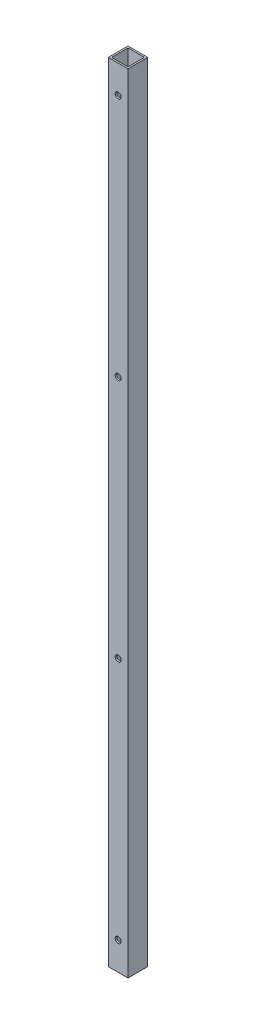
SolidWorks part; units mm, degrees
material "1060 Alloy"
ref_plane "Front Plane" through (0, 0, 0) normal (0, 0, 1) x (1, 0, 0)
ref_plane "Top Plane" through (0, 0, 0) normal (0, 1, 0) x (1, 0, 0)
ref_plane "Right Plane" through (0, 0, 0) normal (1, 0, 0) x (0, 0, -1)
sketch "Sketch1" plane through (0, 0, 0) normal (0, 1, 0) x (1, 0, 0)
  line L1 (-9.5, 9.5) -> (9.5, 9.5)
  line L2 (-9.5, 9.5) -> (-9.5, -9.5)
  line L3 (-9.5, -9.5) -> (9.5, -9.5)
  line L4 (9.5, 9.5) -> (9.5, -9.5)
  line L5 (-9.5, 9.5) -> (9.5, -9.5) construction
  line L6 (-9.5, -9.5) -> (9.5, 9.5) construction
  line L7 (-7.9375, 7.9375) -> (7.9375, 7.9375)
  line L8 (-7.9375, 7.9375) -> (-7.9375, -7.9375)
  line L9 (-7.9375, -7.9375) -> (7.9375, -7.9375)
  line L10 (7.9375, 7.9375) -> (7.9375, -7.9375)
  line L11 (-7.9375, 7.9375) -> (7.9375, -7.9375) construction
  line L12 (-7.9375, -7.9375) -> (7.9375, 7.9375) construction
  point P0 (0, 0)
  point P5 (0, 0)
  dimension "D1" = 19
  dimension "D2" = 19
  dimension "D3" = 15.875
  dimension "D4" = 15.875
extrude "Tube" add sketch "Sketch1" along normal blind 758.9266
sketch "Sketch2" plane through (0, 0, 9.5) normal (0, 0, 1) x (1, 0, 0)
  line L0 (0, 758.9266) -> (0, 777.9766) construction
  line L1 (0, 777.9766) -> (0, 781.05) construction
  line L6 (0, 731.925) -> (0, 758.9266) construction
  line L7 (-9.5, 758.9266) -> (9.5, 758.9266) construction
  circle A2 centre (0, 731.925) radius 2.8956
  dimension "D1" = 5.7912
  dimension "D2" = 19.05
  dimension "D3" = 3.0734
  dimension "D4" = 49.125
extrude "Side Wall Holes" cut sketch "Sketch2" against normal through all
pattern_linear "LPattern1" count 4 spacing 234.9745 along (0, -1, 0) of "Side Wall Holes"
sketch "Sketch3" plane through (-9.5, 0, 0) normal (-1, 0, 0) x (0, 0, 1)
  line L0 (-9.5, 758.9266) -> (9.5, 758.9266) construction
  line L1 (-123.9293, 379.4633) -> (189.6619, 379.4633) construction
  line L2 (-9.5, 0) -> (9.5, 0) construction
  circle A0 centre (0, 674.37) radius 4.7625
  circle A1 centre (0, 84.5566) radius 4.7625
  point P4 (0, 758.9266)
  dimension "D1" = 9.525
  dimension "D2" = 84.5566
extrude "Cut-Extrude1" cut sketch "Sketch3" against normal up to next and the other way through all
equation "\"Height\"= 32in"
equation "\"Width\"= 23in"
equation "\"Depth\"= 20in"
equation "\"Plexi\"= .121in"
equation "\"Cutwidth\"= .016in"
equation "\"Earsize\"= 1in + \"Cutwidth\" /2"
equation "\"Slotsize\" = 1in - \"CutWidth\" / 2"
equation "\"InnerWidth\" = \"Width\" - 2* \"Plexi\""
equation "\"InnerHeight\" = \"Height\" -2 * \"Plexi\""
equation "\"RearHoleSpacing\" = (\"Width\" - 2*\"RearHolesBorder\") / (\"RearNumHoles\"-1)"
equation "\"RivetDia\" = .228in"
equation "\"SlotDepth\" = \"Plexi\" + 0.75in + .005in"
equation "\"SideSlotWidth\"   = \"Plexi\"+.005in"
equation "\"D1@Sketch2\"=\"RivetDia\""
equation "\"D2@Sketch2\"=\"CornerCube\""
equation "\"SidePanelVertSpacing\" = (\"Height\"-2*(1.75-\"Plexi\")) / 5"
equation "\"MagnetThickness\"= 0.125in"
equation "\"MagnetDiameter\"= 12mm"
equation "\"DoorPlexi\" = \"Plexi\""
equation "\"Boxsize\" = .75in"
equation "\"Boxinner\" = .625in"
equation "\"CornerCube\" = 0.75in"
equation "\"FingerLength\" = 1.125in"
equation "\"InnerDepth\" = \"Depth\" - 2*\"Plexi\""
equation "\"RearNumHoles\" = 4"
equation "\"RearHolesBorder\" = 2.25"
equation "\"RearBarLength\" = (\"InnerWidth\"-2*\"CornerCube\")"
equation "\"RearTopNumHoles\" = 4"
equation "\"RearTopHolesBorder\" = 3.1"
equation "\"RearTopHolesSpacing\" = (\"Width\" - 2*\"RearTopHolesBorder\") / (\"RearTopNumHoles\"-1)"
equation "\"SideTopNumHoles\" = 4"
equation "\"SideTopHoleOffset\"=\"CornerCube\"+\"FingerLength\"+\"Plexi\"+.5"
equation "\"SideTopHoleSpacing\" = (\"TopBarDepth\"-2*\"SideTopHoleOffset\") / (\"SideTopNumHoles\"-1)"
equation "\"SideHorizNumHoles\" = 4"
equation "\"SideHorizHoleBorder\" = 1.50"
equation "\"SideHorizHoleSpacing\" = (\"TopBarDepth\"-2*\"SideHorizHoleBorder\") / (\"SideHorizNumHoles\"-1)"
equation "\"SideVertNumHoles\" = 4"
equation "\"SideVertHolesBorder\" = \"CornerCube\"+\"FingerLength\"+1.50"
equation "\"SideVertHoleSpacing\" = (\"SideVertBarLength\" - 2*(\"SideVertHolesBorder\"-\"Plexi\"-\"CornerCube\")) / (\"SideVertNumHoles\"-1)"
equation "\"BottomPanelSideHoleSpacing\" = (\"InnerDepth\"-2*(1.75-\"Plexi\")) / 4"
equation "\"FrontDoorGap\" = .1in"
equation "\"TopDepth\" = \"Depth\"-\"DoorPlexi\"-\"FrontDoorGap\""
equation "\"TopBarDepth\" = \"Depth\"-\"DoorPlexi\"-\"Plexi\"-2*\"MagnetThickness\"-2*\"CornerCube\""
equation "\"D3@Sketch2\"=\"Plexi\""
equation "\"D4@Sketch2\"=\"SideVertHolesBorder\""
equation "\"D3@LPattern1\"=\"SideVertHoleSpacing\""
equation "\"D1@LPattern1\"=\"SideVertNumHoles\""
equation "\"BasePlateThickness\" = 0.5in"
equation "\"SideVertBarLength\"=\"Height\"-\"BasePlateThickness\"-2*\"CornerCube\"-\"Plexi\""
equation "\"RearSideVertNumHoles\" = 4"
equation "\"RearSideVertHolesBorder\" = 2.4"
equation "\"RearSideVertHoleSpacing\" = (\"SideVertBarLength\" - 2*(\"RearSideVertHolesBorder\"-\"Plexi\"-\"CornerCube\")) / (\"RearSideVertNumHoles\"-1)"
equation "\"D1@Tube\"=\"SideVertBarLength\""
equation "\"D3@Sketch1\"=\"Boxinner\""
equation "\"D4@Sketch1\"=\"Boxinner\""
equation "\"EBWidth\" = 9in"
equation "\"BasePlateWidth\" = \"Width\"+\"EBWidth\"-2*\"Plexi\""
equation "\"BasePlateDepth\" = \"TopBarDepth\"+2*\"CornerCube\""
equation "\"BoxsizeHalf\" = \"Boxsize\"/2"
equation "\"FingerWidth\" = .625in"
equation "\"CoolerDepth\" = 12in"
equation "\"ShelfGap\" = 0.5in"
equation "\"ShelfDepth\" = \"TopBarDepth\"+\"CornerCube\"-\"CoolerDepth\""
equation "\"ShelfBarDepth\"=\"ShelfDepth\"-2*\"CornerCube\""
equation "\"ShelfWidth\" = \"EBWidth\"-\"ShelfGap\""
equation "\"ShelfBarWidth\" = \"EBWidth\"-\"Boxsize\""
equation "\"ShelfBarWidthShort\" = \"ShelfBarWidth\"-\"Boxsize\"-\"ShelfGap\""
equation "\"IntakeWidth\"=4in"
equation "\"IntakeHeight\"=2in"
equation "\"ExhaustWidth\"=4in"
equation "\"ExhaustHeight\"=2in"
equation "\"VentSpacing\"=7in"
equation "\"AngleBracketLength\"=20mm"
equation "\"AngleBracketWidth\"=.5in"
equation "\"AngleBracketThickness\"=.125in"
equation "\"AngleBracketHolePos\"=15mm"
equation "\"AngleBracketHoleDia\"=\"Rivet3_16Dia\""
equation "\"ShelfBarAngleHole\"=\"ShelfGap\"+\"Boxsize\"+\"AngleBracketHolePosShort\""
